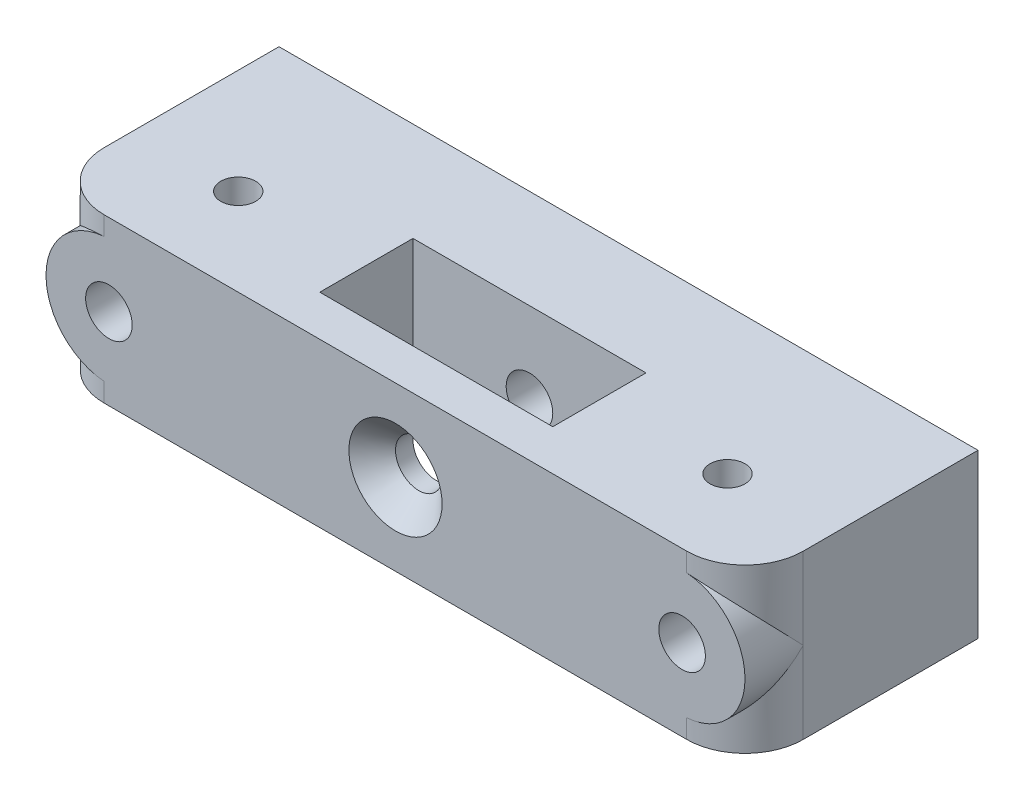
SolidWorks part; units mm, degrees
material "ABS"
ref_plane "Спереди" through (0, 0, 0) normal (0, 0, 1) x (1, 0, 0)
ref_plane "Сверху" through (0, 0, 0) normal (0, 1, 0) x (1, 0, 0)
ref_plane "Справа" through (0, 0, 0) normal (1, 0, 0) x (0, 0, -1)
sketch "Эскиз1" plane through (0, 0, 0) normal (0, 0, 1) x (1, 0, 0)
  line L1 (30, -7) -> (-30, -7)
  line L2 (30, -7) -> (30, 7)
  line L3 (30, 7) -> (-30, 7)
  line L4 (-30, -7) -> (-30, 7)
  line L5 (30, -7) -> (-30, 7) construction
  line L6 (30, 7) -> (-30, -7) construction
  point P0 (0, 0)
  dimension "D1" = 60
  dimension "D2" = 14
extrude "Бобышка-Вытянуть1" add sketch "Эскиз1" along normal blind 20
sketch "Эскиз2" plane through (0, -7, 0) normal (0, -1, 0) x (-1, 0, 0)
  line L0 (0, -20) -> (0, 0) construction
  line L1 (30, -20) -> (-30, -20) construction
  line L2 (8.5, -12.5) -> (-8.5, -12.5) construction
  line L3 (-10, -8.5) -> (10, -8.5)
  line L4 (-10, -8.5) -> (-10, -16.5)
  line L5 (-10, -16.5) -> (10, -16.5)
  line L6 (10, -8.5) -> (10, -16.5)
  line L7 (-10, -8.5) -> (10, -16.5) construction
  line L8 (-10, -16.5) -> (10, -8.5) construction
  line L11 (0, 4) -> (0, -7.5) construction
  line L13 (-8.5, -14.75) -> (-8.5, -10.25) construction
  line L14 (8.5, -14.75) -> (8.5, -10.25) construction
  point P5 (0, -12.5)
  dimension "D1" = 20
  dimension "D2" = 8
extrude "Вырез-Вытянуть1" cut sketch "Эскиз2" against normal through all
sketch "Эскиз3" plane through (0, 7, 0) normal (0, 1, 0) x (1, 0, 0)
  circle A0 centre (-21, -12.5) radius 1.5
  circle A1 centre (21, -12.5) radius 1.5
  dimension "D1" = 3
extrude "Вырез-Вытянуть2" cut sketch "Эскиз3" against normal blind 10.5
fillet "Скругление1" radius 5 2 edges at (-30, 0, 20) (30, 0, 20)
sketch "Эскиз4" plane through (0, 0, 20) normal (0, 0, 1) x (1, 0, 0)
  line L0 (-30, 0) -> (30, 0) construction
  line L1 (-30, -7) -> (-30, 7) construction
  line L2 (30, 7) -> (30, -7) construction
  line L3 (0, 7) -> (0, -7) construction
  line L4 (25, 7) -> (-25, 7) construction
  line L6 (-25, -7) -> (25, -7) construction
  circle A0 centre (24.6, 0) radius 2
  circle A1 centre (-24.6, 0) radius 2
  circle A2 centre (0, 0) radius 2
  dimension "D1" = 4
  dimension "D3" = 4
  dimension "D2" = 5.4
extrude "Вырез-Вытянуть3" cut sketch "Эскиз4" against normal through all
chamfer "Фаска1" distance 2 angle 45 1 edges at (2, 0, 20)
sketch "Эскиз5" plane through (0, 0, 20) normal (0, 0, 1) x (1, 0, 0)
  line L0 (-30, -7) -> (-30, 7) construction
  line L1 (30, 7) -> (30, -7) construction
  circle A0 centre (-24.6, 0) radius 5.4
  circle A1 centre (24.6, 0) radius 5.4
  circle A2 centre (24.6, 0) radius 2
  circle A3 centre (-24.6, 0) radius 2
  arc A4 (25, 1.9596) -> (25, -1.9596) centre (24.6, 0) ccw construction
extrude "Бобышка-Вытянуть2" add sketch "Эскиз5" against normal blind 5.5
